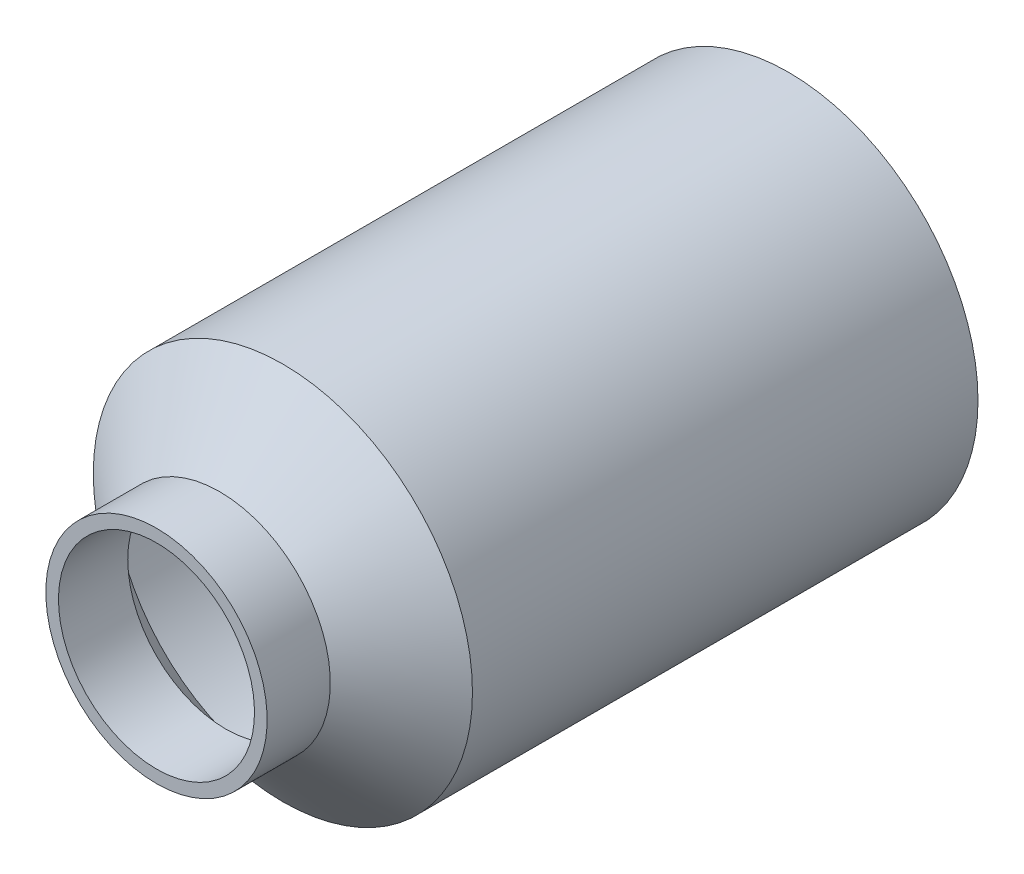
SolidWorks part; units mm, degrees
ref_plane "Front Plane" through (0, 0, 0) normal (1, 0, 0) x (0, 1, 0)
ref_plane "Top Plane" through (0, 0, 0) normal (0, 0, 1) x (0, 1, 0)
ref_plane "Right Plane" through (0, 0, 0) normal (0, 1, 0) x (-1, 0, 0)
sketch "Sketch1" plane through (0, 0, 0) normal (1, 0, 0) x (0, 1, 0)
  line L0 (0, 0) -> (0, 101.6)
  line L1 (0, 101.6) -> (15.8623, 114.3)
  line L2 (15.8623, 114.3) -> (15.8623, 127)
  line L3 (15.8623, 127) -> (38.1, 127)
  line L4 (38.1, 127) -> (38.1, 0)
  line L5 (38.1, 0) -> (0, 0)
  dimension "D1" = 38.1
  dimension "D2" = 127
  dimension "D3" = 101.6
  dimension "D4" = 12.7
  dimension "D5" = 20.32
revolve "Revolve1" add sketch "Sketch1" angle 360 about L4
shell "Shell1" thickness 2.54
